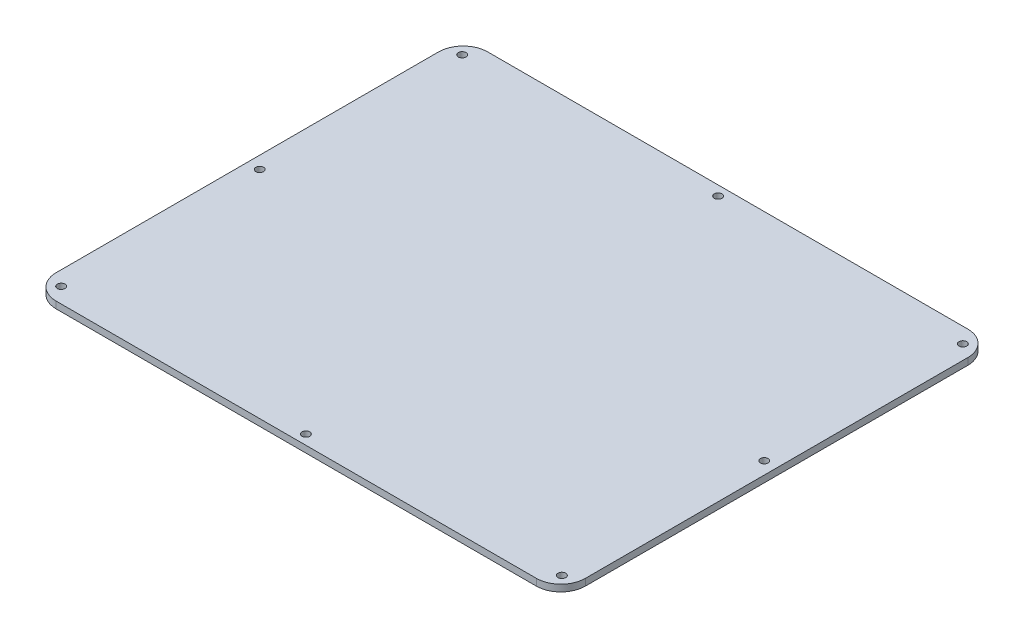
SolidWorks part; units mm, degrees
ref_plane "Front Plane" through (0, 0, 0) normal (0, 0, 1) x (1, 0, 0)
ref_plane "Top Plane" through (0, 0, 0) normal (0, 1, 0) x (1, 0, 0)
ref_plane "Right Plane" through (0, 0, 0) normal (1, 0, 0) x (0, 0, -1)
sketch "Sketch1" plane through (0, 0, 0) normal (0, 1, 0) x (1, 0, 0)
  line L1 (-156.0187, 99.0458) -> (117.4813, 99.0458)
  line L2 (-156.0187, 99.0458) -> (-156.0187, -123.9542)
  line L3 (-156.0187, -123.9542) -> (117.4813, -123.9542)
  line L4 (117.4813, 99.0458) -> (117.4813, -123.9542)
  dimension "D1" = 273.5
  dimension "D2" = 223
extrude "Boss-Extrude1" add sketch "Sketch1" along normal blind 3.5
fillet "Fillet1" radius 12.7 4 edges at (-156.0187, 1.75, 123.9542) (-156.0187, 1.75, -99.0458) (117.4813, 1.75, -99.0458) (117.4813, 1.75, 123.9542)
sketch "Sketch2" plane through (0, 3.5, 0) normal (0, 1, 0) x (1, 0, 0)
  line L0 (-19.2687, -123.9542) -> (-19.2687, 99.0458) construction
  line L1 (-143.3187, -123.9542) -> (104.7813, -123.9542) construction
  line L2 (104.7813, 99.0458) -> (-143.3187, 99.0458) construction
  line L3 (-156.0187, -12.4542) -> (117.4813, -12.4542) construction
  line L4 (-156.0187, 86.3458) -> (-156.0187, -111.2542) construction
  line L5 (117.4813, -111.2542) -> (117.4813, 86.3458) construction
  circle A0 centre (-19.2687, 94.0458) radius 2
  circle A1 centre (-148.6187, 91.1458) radius 2
  circle A2 centre (110.0813, 91.1458) radius 2
  circle A3 centre (-148.6187, 91.1458) radius 2
  circle A4 centre (110.0813, 91.1458) radius 2
  circle A5 centre (110.0813, -116.0542) radius 2
  circle A6 centre (-148.6187, -116.0542) radius 2
  circle A7 centre (110.0813, -116.0542) radius 2
  circle A8 centre (-148.6187, -116.0542) radius 2
  circle A9 centre (-19.2687, -118.9542) radius 2
  circle A10 centre (111.0813, -12.4542) radius 2
  circle A11 centre (111.0813, -12.4542) radius 2
  circle A12 centre (-149.6187, -12.4542) radius 2
  point P31 (104.3624, -12.4542)
  point P34 (0, 0)
  dimension "D1" = 5
  dimension "D3" = 7.9
  dimension "D4" = 129.35
  dimension "D5" = 6.4
extrude "Cut-Extrude1" cut sketch "Sketch2" against normal blind 3.5 contours A6 | A12 | A1 | A0 | A10 | A2 | A5 | A9
